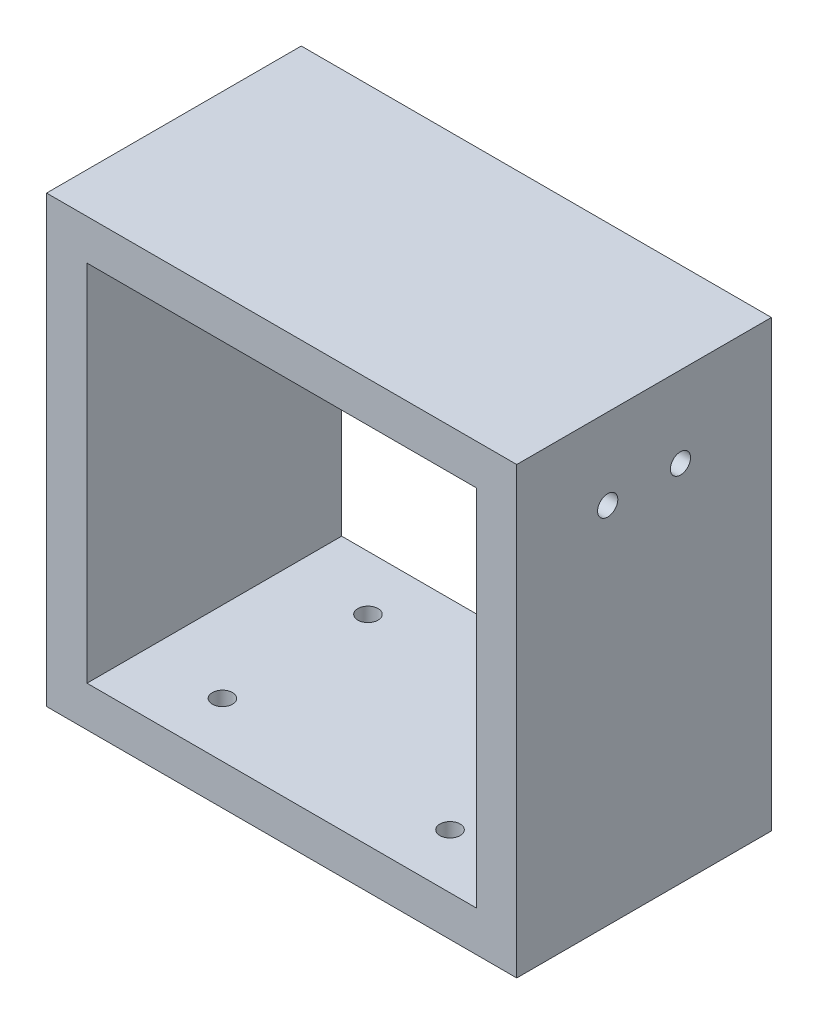
SolidWorks part; units mm, degrees
ref_plane "前视基准面" through (0, 0, 0) normal (0, 0, 1) x (1, 0, 0)
ref_plane "上视基准面" through (0, 0, 0) normal (0, 1, 0) x (1, 0, 0)
ref_plane "右视基准面" through (0, 0, 0) normal (1, 0, 0) x (0, 0, -1)
sketch "草图1" plane through (0, 0, 0) normal (0, 1, 0) x (1, 0, 0)
  line L1 (0, 0) -> (58.15, 0)
  line L2 (0, 0) -> (0, 31.5)
  line L3 (0, 31.5) -> (58.15, 31.5)
  line L4 (58.15, 0) -> (58.15, 31.5)
  dimension "D1" = 58.15
  dimension "D2" = 31.5
extrude "凸台-拉伸1" add sketch "草图1" against normal blind 55
sketch "草图2" plane through (0, 0, 0) normal (0, 0, 1) x (1, 0, 0)
  line L0 (0, -27.5) -> (53.15, -27.5) construction
  line L1 (0, -55) -> (0, 0) construction
  line L2 (29.075, 0) -> (29.075, -40.7336) construction
  line L3 (0, 0) -> (58.15, 0) construction
  line L4 (58.15, -55) -> (58.15, 0) construction
  line L5 (5, -50) -> (53.15, -50)
  line L6 (5, -50) -> (5, -5)
  line L7 (5, -5) -> (53.15, -5)
  line L8 (53.15, -50) -> (53.15, -5)
  line L9 (29.075, -5) -> (29.075, -50) construction
  line L10 (5, -27.5) -> (53.15, -27.5) construction
  point P8 (29.075, -27.5)
  dimension "D1" = 5
  dimension "D2" = 5
  dimension "D3" = 5
extrude "切除-拉伸1" cut sketch "草图2" against normal up to surface (31.5 mm away) up to face at (29.075, -27.5, -31.5)
sketch "草图4" plane through (0, -55, 0) normal (0, -1, 0) x (1, 0, 0)
  circle A0 centre (15, -6.75) radius 1.25
  circle A2 centre (43.15, -6.75) radius 1.25
extrude "切除-拉伸2" cut sketch "草图4" against normal blind 10
sketch "草图5" plane through (0, -55, 0) normal (0, -1, 0) x (1, 0, 0)
  circle A0 centre (43.15, -24.75) radius 1.25
  circle A1 centre (15, -24.75) radius 1.25
extrude "切除-拉伸3" cut sketch "草图5" against normal blind 10
sketch "草图6" plane through (5, 0, 0) normal (1, 0, 0) x (0, 0, -1)
  circle A0 centre (11.25, -10) radius 1.25
  circle A1 centre (20.25, -10) radius 1.25
  point P4 (0, 0)
  dimension "D1" = 2.5
  dimension "D2" = 2.5
extrude "切除-拉伸4" cut sketch "草图6" against normal blind 20.7
sketch "草图7" plane through (58.15, 0, 0) normal (1, 0, 0) x (0, 0, -1)
  circle A0 centre (20.25, -10) radius 1.25
  circle A1 centre (11.25, -10) radius 1.25
  point P4 (0, 0)
  point P5 (0, 0)
  dimension "D1" = 2.5
  dimension "D2" = 2.5
extrude "切除-拉伸5" cut sketch "草图7" against normal blind 20.7
